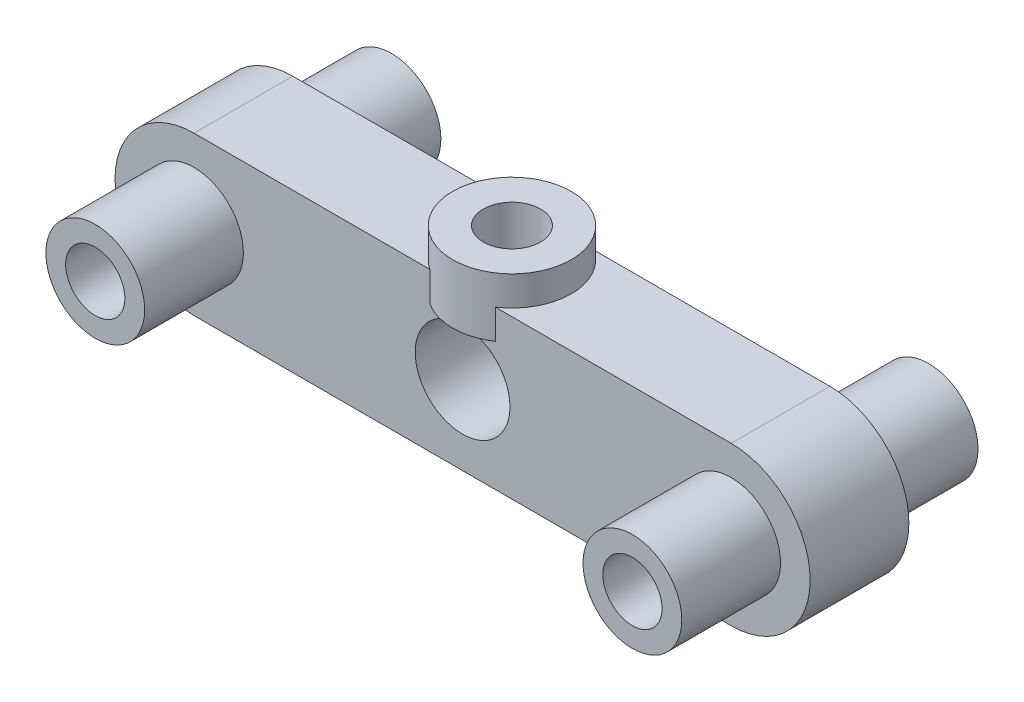
SolidWorks part; units mm, degrees
ref_plane "Front Plane" through (0, 0, 0) normal (0, 0, 1) x (1, 0, 0)
ref_plane "Top Plane" through (0, 0, 0) normal (0, 1, 0) x (1, 0, 0)
ref_plane "Right Plane" through (0, 0, 0) normal (1, 0, 0) x (0, 0, -1)
sketch "Sketch1" plane through (0, 0, 0) normal (0, 0, 1) x (1, 0, 0)
  line L0 (0, 0) -> (27.2, 0) construction
  line L1 (0, 4) -> (27.2, 4)
  line L2 (0, -4) -> (27.2, -4)
  arc A0 (0, 4) -> (0, -4) centre (0, 0) ccw
  arc A1 (27.2, -4) -> (27.2, 4) centre (27.2, 0) ccw
  circle A2 centre (0, 0) radius 5.5 construction
  circle A3 centre (13.6, 0) radius 2.4
  point P3 (13.6, 0)
  dimension "D1" = 11
  dimension "D2" = 4
  dimension "D3" = 27.2
  dimension "D4" = 4.8
extrude "Boss-Extrude1" add sketch "Sketch1" along normal blind 5 contours L1 A1 L2 A0
sketch "Sketch5" plane through (0, 4, 0) normal (0, 1, 0) x (1, 0, 0)
  line L0 (13.6, -5) -> (13.6, 3.7333) construction
  line L1 (27.2, -5) -> (0, -5) construction
  circle A0 centre (13.6, -2.5) radius 3
  dimension "D1" = 2.5
  dimension "D2" = 6
extrude "Boss-Extrude3" add sketch "Sketch5" against normal mid plane 3
sketch "Sketch6" plane through (0, 0, 5) normal (0, 0, 1) x (1, 0, 0)
  line L0 (13.6, 0) -> (13.6, 14.0979) construction
  circle A0 centre (27.2, 0) radius 1.45
  circle A1 centre (0, 0) radius 1.45
  dimension "D1" = 2.9
extrude "Cut-Extrude4" cut sketch "Sketch6" against normal blind 9
sketch "Sketch2" plane through (0, 4, 0) normal (0, 1, 0) x (1, 0, 0)
  line L0 (27.2, 0) -> (15.2583, 0) construction
  line L2 (13.6, -4.9497) -> (13.6, 4.5675) construction
  line L4 (0, -5) -> (0, 0) construction
  circle A0 centre (13.6, -2.5) radius 1.45
  dimension "D1" = 2.9
  dimension "D3" = 13.6
  dimension "D2" = 2.5
extrude "Cut-Extrude3" cut sketch "Sketch2" against normal mid plane 8 contours A0
sketch "Sketch7" plane through (0, 0, 5) normal (0, 0, 1) x (1, 0, 0)
  circle A0 centre (27.2, 0) radius 2.5
  circle A1 centre (27.2, 0) radius 1.5
  circle A2 centre (0, 0) radius 2.5
  circle A3 centre (0, 0) radius 1.5
  dimension "D1" = 5
  dimension "D2" = 5
  dimension "D3" = 3
  dimension "D4" = 3
extrude "Boss-Extrude4" add sketch "Sketch7" along normal blind 5
ref_plane "Plane1" through (0, 0, 2.5) normal (0, 0, -1) x (-1, 0, 0)
mirror "Mirror1" about plane through (0, 0, 2.5) normal (0, 0, -1) of "Cut-Extrude4", "Boss-Extrude4"
